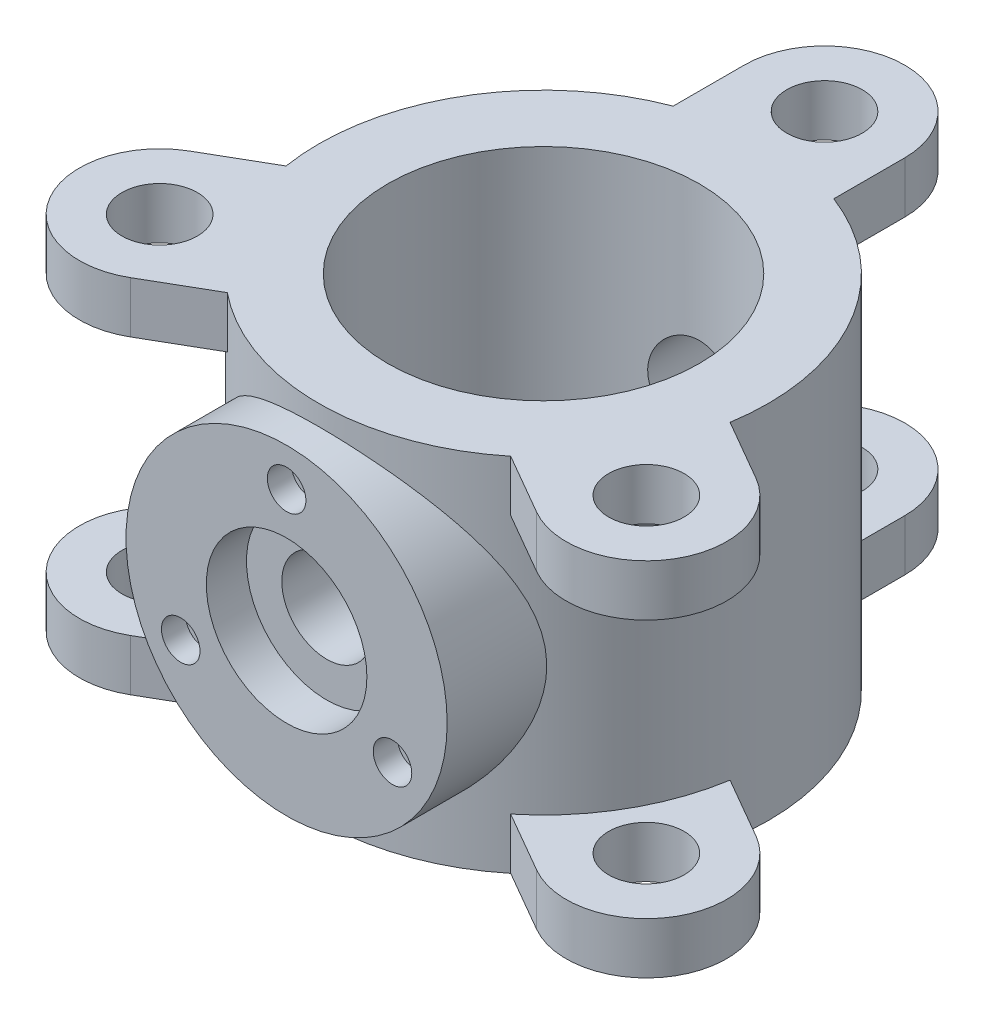
SolidWorks part; units mm, degrees
ref_plane "Front Plane" through (0, 0, 0) normal (0, 0, 1) x (1, 0, 0)
ref_plane "Top Plane" through (0, 0, 0) normal (0, 1, 0) x (1, 0, 0)
ref_plane "Right Plane" through (0, 0, 0) normal (1, 0, 0) x (0, 0, -1)
sketch "Sketch1" plane through (0, 0, 0) normal (0, 0, 1) x (1, 0, 0)
  line L0 (97, 225) -> (97, 0)
  line L1 (97, 0) -> (140, 0)
  line L3 (97, 225) -> (140, 225)
  line L4 (140, 0) -> (140, 225)
  line L5 (0, 0) -> (0, 220.5167) construction
  dimension "D3" = 225
revolve "Revolve1" add sketch "Sketch1" angle 360 about L5
sketch "Sketch2" plane through (0, 225, 0) normal (0, 1, 0) x (1, 0, 0)
  line L0 (-50, 175) -> (-50, 130.767)
  line L1 (50, 175) -> (50, 130.767)
  arc A0 (50, 175) -> (-50, 175) centre (0, 175) ccw
  circle A1 centre (0, 0) radius 140 construction
  circle A2 centre (0, 175) radius 23.5
  point P9 (0, 0)
  circle M2 centre (0, 0) radius 140
  dimension "D2" = 50
  dimension "D3" = 47
  dimension "D1" = 175
extrude "Boss-Extrude1" add sketch "Sketch2" against normal blind 32 contours L1 A0 L0 A2 M2
pattern_circular "CirPattern1" count 3 over 360 about axis through (0, 0, 0) along (0, 1, 0) of "Boss-Extrude1"
sketch "Sketch3" plane through (0, 0, 0) normal (0, 1, 0) x (1, 0, 0)
  line L0 (-50, 175) -> (-50, 130.767)
  line L1 (50, 175) -> (50, 130.767)
  arc A0 (50, 175) -> (-50, 175) centre (0, 175) ccw
  circle A2 centre (0, 175) radius 23.5
  point P9 (0, 0)
  circle M9 centre (0, 0) radius 140
  dimension "D2" = 50
  dimension "D3" = 47
extrude "Boss-Extrude2" add sketch "Sketch3" along normal blind 32 contours A0 L1 L0 A2 M9
pattern_circular "CirPattern2" count 3 over 360 about axis through (0, 0, 0) along (0, 1, 0) of "Boss-Extrude2"
ref_plane "Plane1" through (0, 0, 140) normal (0, 0, 1) x (1, 0, 0)
sketch "Sketch5" plane through (0, 0, 140) normal (0, 0, 1) x (1, 0, 0)
  line L0 (0, 0) -> (0, 225) construction
  line L1 (88.2475, 225) -> (-88.2475, 225) construction
  circle A0 centre (0, 112.5) radius 100
  dimension "D1" = 200
extrude "Boss-Extrude4" add sketch "Sketch5" against normal blind 62 from offset 20
sketch "Sketch6" plane through (0, 0, 160) normal (0, 0, 1) x (1, 0, 0)
  line L0 (0, 212.5) -> (0, 12.5) construction
  arc A0 (99.98, 114.5) -> (-99.98, 114.5) centre (0, 112.5) ccw construction
  arc A1 (-99.98, 110.5) -> (99.98, 110.5) centre (0, 112.5) ccw construction
  circle A2 centre (0, 112.5) radius 50
  dimension "D1" = 100
extrude "Cut-Extrude2" cut sketch "Sketch6" against normal blind 25
sketch "Sketch4" plane through (0, 0, 140) normal (0, 0, 1) x (1, 0, 0)
  line L0 (0, 0) -> (0, 225) construction
  line L1 (88.2475, 225) -> (-88.2475, 225) construction
  circle A0 centre (0, 112.5) radius 28
  dimension "D1" = 56
extrude "Cut-Extrude1" cut sketch "Sketch4" against normal blind 342
sketch "Sketch7" plane through (0, 0, 160) normal (0, 0, 1) x (1, 0, 0)
  line L0 (0, 212.5) -> (0, 12.5) construction
  arc A0 (99.98, 114.5) -> (-99.98, 114.5) centre (0, 112.5) ccw construction
  arc A1 (-99.98, 110.5) -> (99.98, 110.5) centre (0, 112.5) ccw construction
  circle A2 centre (0, 188.646) radius 12
  dimension "D1" = 24
extrude "Cut-Extrude3" cut sketch "Sketch7" against normal blind 15
pattern_circular "CirPattern3" count 3 over 360 about axis through (0, 112.5, 0) along (0, 0, 1) of "Cut-Extrude3"
